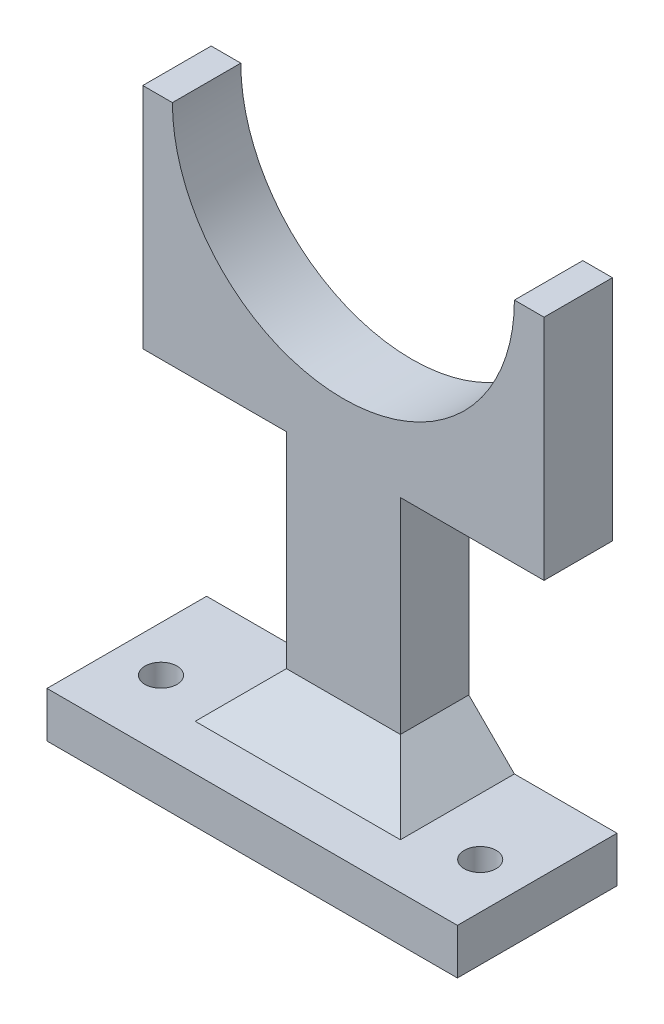
SolidWorks part; units mm, degrees
ref_plane "前基準面" through (0, 0, 0) normal (0, 0, 1) x (1, 0, 0)
ref_plane "上基準面" through (0, 0, 0) normal (0, 1, 0) x (1, 0, 0)
ref_plane "右基準面" through (0, 0, 0) normal (1, 0, 0) x (0, 0, -1)
sketch "草圖1" plane through (0, 0, 0) normal (0, 0, 1) x (1, 0, 0)
  line L1 (-63.3705, -30.5) -> (26.6295, -30.5)
  line L2 (-63.3705, -30.5) -> (-63.3705, -40.5)
  line L3 (-63.3705, -40.5) -> (26.6295, -40.5)
  line L4 (26.6295, -30.5) -> (26.6295, -40.5)
  line L5 (-30.8705, -30.5) -> (-5.8705, -30.5)
  line L6 (-30.8705, -30.5) -> (-30.8705, 24.5)
  line L7 (-30.8705, 24.5) -> (-5.8705, 24.5)
  line L8 (-5.8705, -30.5) -> (-5.8705, 24.5)
  line L9 (-62.3705, 74.5) -> (25.6295, 74.5)
  line L10 (-62.3705, 74.5) -> (-62.3705, 24.5)
  line L11 (-62.3705, 24.5) -> (25.6295, 24.5)
  line L12 (25.6295, 74.5) -> (25.6295, 24.5)
  circle A0 centre (-18.3705, 74.5) radius 37.5
  dimension "D3" = 75
  dimension "D6" = 90
  dimension "D1" = 50
  dimension "D2" = 88
  dimension "D4" = 25
  dimension "D5" = 31.5
  dimension "D7" = 55
  dimension "D8" = 32.5
  dimension "D9" = 10
extrude "填料-伸長1" add sketch "草圖1" along normal blind 15 contours A0 L9 L10 L11 L7 L12 | L1 L8 L7 L6 | L4 L1 L2 L3
sketch "草圖2" plane through (0, 0, 15) normal (0, 0, 1) x (1, 0, 0)
  line L1 (-63.3705, -30.5) -> (26.6295, -30.5)
  line L2 (-63.3705, -30.5) -> (-63.3705, -40.5)
  line L3 (-63.3705, -40.5) -> (26.6295, -40.5)
  line L4 (26.6295, -30.5) -> (26.6295, -40.5)
extrude "填料-伸長2" add sketch "草圖2" along normal blind 20
chamfer "導角4" distance 10 angle 45 3 edges at (-5.8705, -30.5, 7.5) (-18.3705, -30.5, 15) (-30.8705, -30.5, 7.5)
sketch "草圖4" plane through (0, -30.5, 0) normal (0, 1, 0) x (1, 0, 0)
  line L0 (-63.3705, -35) -> (-63.3705, 0) construction
  line L2 (26.6295, -35) -> (-63.3705, -35) construction
  line L3 (26.6295, -35) -> (26.6295, 0) construction
  circle A0 centre (-53.3705, -20) radius 2
  circle A1 centre (16.6295, -20) radius 2
  point P8 (-53.951, -35)
  dimension "D3" = 4
  dimension "D4" = 4
  dimension "D5" = 10
  dimension "D6" = 15
  dimension "D1" = 10
  dimension "D2" = 15
extrude "除料-伸長1" cut sketch "草圖4" against normal through all
sketch "草圖5" plane through (0, -30.5, 0) normal (0, 1, 0) x (1, 0, 0)
  circle A0 centre (-53.3705, -20) radius 3.5
  circle A1 centre (16.6295, -20) radius 3.5
  dimension "D1" = 7
  dimension "D2" = 7
extrude "除料-伸長2" cut sketch "草圖5" against normal blind 7
